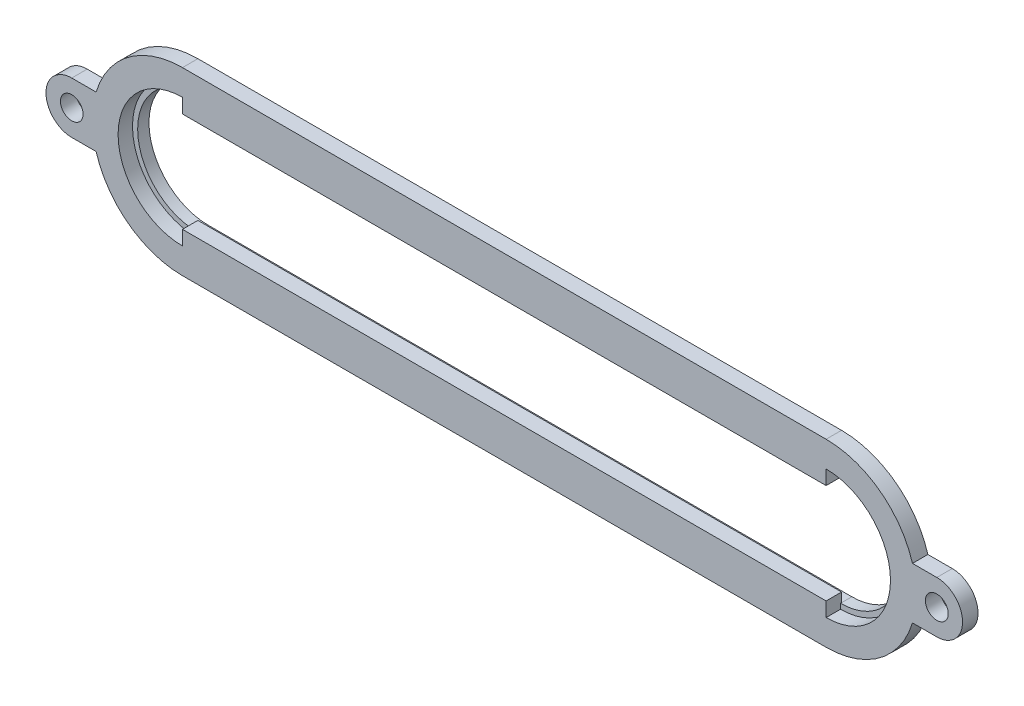
SolidWorks part; units mm, degrees
ref_plane "Front Plane" through (0, 0, 0) normal (0, 0, 1) x (1, 0, 0)
ref_plane "Top Plane" through (0, 0, 0) normal (0, 1, 0) x (1, 0, 0)
ref_plane "Right Plane" through (0, 0, 0) normal (1, 0, 0) x (0, 0, -1)
sketch "Sketch1" plane through (0, 0, 0) normal (0, 0, 1) x (1, 0, 0)
  line L0 (177.8806, -12.319) -> (177.8806, -15.875)
  line L26 (19.1306, 22.225) -> (177.8806, 22.225)
  line L30 (19.1306, -22.225) -> (177.8806, -22.225)
  line L31 (19.1306, 15.875) -> (19.1306, 12.319)
  line L32 (19.1306, 12.319) -> (177.8806, 12.319)
  line L33 (177.8806, 22.225) -> (19.1306, 22.225)
  line L36 (19.1306, -22.225) -> (177.8806, -22.225)
  line L37 (177.8806, 12.319) -> (19.1306, 12.319)
  line L38 (19.1306, -12.319) -> (177.8806, -12.319)
  line L39 (19.1306, 15.875) -> (19.1306, 12.319)
  line L40 (177.8806, 15.875) -> (177.8806, 12.319)
  line L41 (19.1306, -12.319) -> (19.1306, -15.875)
  line L42 (177.8806, 15.875) -> (19.1306, 15.875) construction
  line L43 (19.1306, -15.875) -> (177.8806, -15.875) construction
  line L44 (177.8806, 12.319) -> (177.8806, 15.875)
  line L45 (19.1306, -15.875) -> (19.1306, -12.319)
  line L46 (19.1306, -12.319) -> (177.8806, -12.319)
  line L47 (49.0118, -102.2086) -> (170.9448, -102.2086)
  line L48 (49.0118, -102.2086) -> (49.0118, -133.3558)
  line L49 (49.0118, -133.3558) -> (170.9448, -133.3558)
  line L50 (170.9448, -102.2086) -> (170.9448, -133.3558)
  arc A12 (177.8806, -15.875) -> (177.8806, 15.875) centre (177.8806, 0) ccw
  arc A13 (19.1306, -15.875) -> (19.1306, 15.875) centre (19.1306, 0) cw
  arc A17 (19.1306, -22.225) -> (19.1306, 22.225) centre (19.1306, 0) cw
  arc A18 (177.8806, -22.225) -> (177.8806, 22.225) centre (177.8806, 0) ccw
  arc A21 (19.1306, -12.319) -> (19.1306, 12.319) centre (19.1306, 0) cw construction
  arc A22 (177.8806, -12.319) -> (177.8806, 12.319) centre (177.8806, 0) ccw construction
  circle A23 centre (109.9783, -117.7822) radius 10.4138
  arc A24 (19.1306, 22.225) -> (19.1306, -22.225) centre (19.1306, 0) ccw
  arc A25 (177.8806, -22.225) -> (177.8806, 22.225) centre (177.8806, 0) ccw
  dimension "D1" = 6.35
extrude "Boss-Extrude5" add sketch "Sketch1" along normal blind 3.81 contours L30 A18 L26 A17 L41 A13 L31 L32 L40 A12 L0 L38
sketch "Sketch2" plane through (0, 0, 0) normal (0, 0, -1) x (-1, 0, 0)
  line L8 (-177.8806, 14.605) -> (-19.1306, 14.605)
  line L9 (-177.8806, 15.875) -> (-19.1306, 15.875)
  line L17 (-19.1306, 14.605) -> (-19.1306, 14.6652)
  line L23 (-19.1306, 14.605) -> (-19.1306, 14.6652)
  line L28 (-19.1306, 14.6652) -> (-19.1306, 14.605)
  line L29 (-177.8806, -15.875) -> (-19.1306, -15.875)
  line L31 (-177.8806, -14.605) -> (-19.1306, -14.605)
  arc A0 (-177.8806, -15.875) -> (-177.8806, 15.875) centre (-177.8806, 0) cw
  arc A1 (-19.1306, -15.875) -> (-19.1306, 15.875) centre (-19.1306, 0) ccw
  arc A2 (-177.8806, -14.605) -> (-177.8806, 14.605) centre (-177.8806, 0) cw
  arc A3 (-19.1306, -14.605) -> (-19.1306, 14.605) centre (-19.1306, 0) ccw
  line M3 (-19.1306, -15.875) -> (-19.1306, -12.319)
  line M5 (-177.8806, -12.319) -> (-177.8806, -15.875)
  arc M6 (-177.8806, -15.875) -> (-177.8806, 15.875) centre (-177.8806, 0) cw
  line M7 (-177.8806, 15.875) -> (-177.8806, 12.319)
  line M9 (-19.1306, 12.319) -> (-19.1306, 15.875)
  arc M10 (-19.1306, 15.875) -> (-19.1306, -15.875) centre (-19.1306, 0) cw
  dimension "D1" = 1.27
  dimension "D2" = 1.27
extrude "Boss-Extrude14" add sketch "Sketch2" along normal blind 2.54 and the other way blind 0.254 contours A2 M5 M7 M6 | L9 L8 M7 M9 | L31 L29 M5 M3 | A3 M3 M10 M9
sketch "Sketch3" plane through (0, 0, 3.81) normal (0, 0, 1) x (1, 0, 0)
  line L8 (-8.1744, 6.35) -> (-2.168, 6.35)
  line L9 (-8.1744, -6.35) -> (-2.168, -6.35)
  line L12 (205.1856, -6.35) -> (199.1791, -6.35)
  line L13 (205.1856, 6.35) -> (199.1791, 6.35)
  arc A2 (-2.168, 6.35) -> (-2.168, -6.35) centre (19.1306, 0) ccw
  circle A4 centre (-8.1744, 0) radius 2.794
  arc A7 (-8.1744, 6.35) -> (-8.1744, -6.35) centre (-8.1744, 0) ccw
  circle A8 centre (205.1856, 0) radius 2.8205
  arc A9 (205.1856, -6.35) -> (205.1856, 6.35) centre (205.1856, 0) ccw
  arc A11 (199.1791, -6.35) -> (199.1791, 6.35) centre (177.8806, 0) ccw
extrude "Boss-Extrude15" add sketch "Sketch3" against normal blind 3.81
